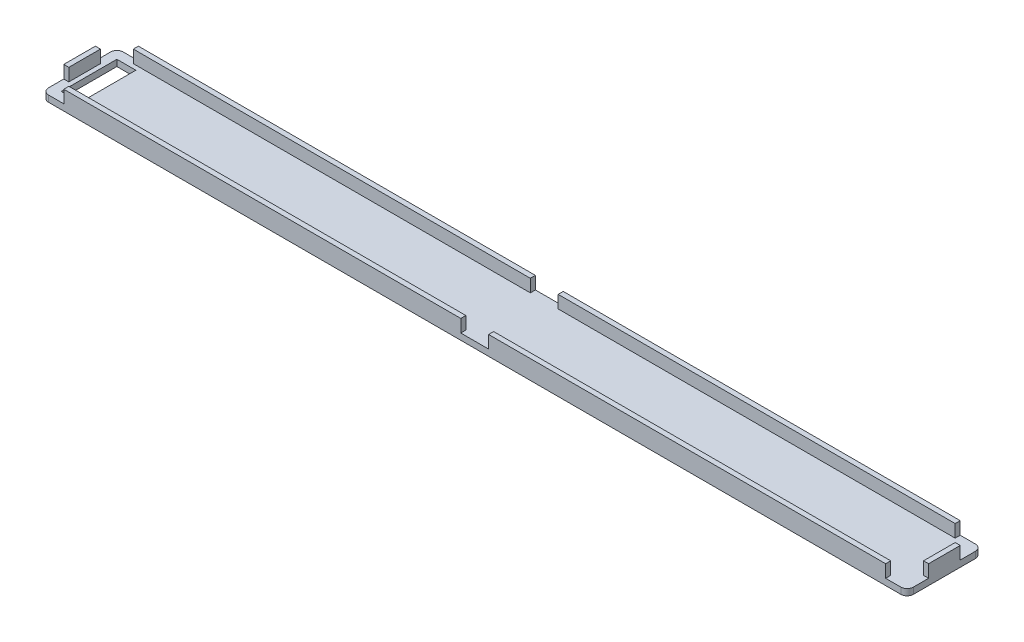
SolidWorks part; units mm, degrees
ref_plane "Plan de face" through (0, 0, 0) normal (0, 0, 1) x (1, 0, 0)
ref_plane "Plan de dessus" through (0, 0, 0) normal (0, 1, 0) x (1, 0, 0)
ref_plane "Plan de droite" through (0, 0, 0) normal (1, 0, 0) x (0, 0, -1)
sketch "Esquisse1" plane through (0, 0, 0) normal (0, 1, 0) x (1, 0, 0)
  line L1 (0, 0) -> (136.8, 0)
  line L2 (0, 0) -> (0, 11.8)
  line L3 (0, 11.8) -> (136.8, 11.8)
  line L4 (136.8, 0) -> (136.8, 11.8)
  dimension "D1" = 11.8
  dimension "D2" = 136.8
extrude "Boss.-Extru.1" add sketch "Esquisse1" along normal blind 1
sketch "Esquisse4" plane through (0, 1, 0) normal (0, 1, 0) x (1, 0, 0)
  line L0 (136, 11) -> (136, 0.8)
  line L1 (136.8, 11.8) -> (0, 11.8)
  line L2 (136.8, 11.8) -> (136.8, 0)
  line L3 (136.8, 0) -> (0, 0)
  line L4 (0, 11.8) -> (0, 0)
  line L5 (136, 0.8) -> (0.8, 0.8)
  line L6 (0.8, 11) -> (0.8, 0.8)
  line L7 (136, 11) -> (0.8, 11)
  dimension "D1" = 0.8
extrude "Boss.-Extru.3" add sketch "Esquisse4" along normal blind 2
sketch "Esquisse5" plane through (0, 3, 0) normal (0, 1, 0) x (1, 0, 0)
  line L0 (136.8, 11.8) -> (136.8, 8.4)
  line L1 (136.8, 0) -> (136.8, 11.8) construction
  line L2 (136.8, 8.4) -> (136, 8.4)
  line L3 (136, 0.8) -> (136, 11) construction
  line L4 (136, 8.4) -> (136, 11)
  line L5 (136, 11) -> (133.4, 11)
  line L6 (136, 11) -> (0.8, 11) construction
  line L7 (133.4, 11) -> (133.4, 11.8)
  line L8 (136.8, 11.8) -> (0, 11.8) construction
  line L9 (133.4, 11.8) -> (136.8, 11.8)
  line L10 (136.8, 5.9) -> (0, 5.9) construction
  line L11 (0, 11.8) -> (0, 0) construction
  line L12 (0, 0) -> (136.8, 0) construction
  line L13 (68.4, 11.8) -> (68.4, 0) construction
  line L14 (3.4, 11.8) -> (0, 11.8)
  line L15 (70.6, 11.8) -> (66.2, 11.8)
  line L16 (70.6, 11.8) -> (70.6, 11)
  line L17 (70.6, 11) -> (66.2, 11)
  line L18 (66.2, 11.8) -> (66.2, 11)
  line L19 (3.4, 11) -> (3.4, 11.8)
  line L20 (0.8, 11) -> (3.4, 11)
  line L21 (0.8, 8.4) -> (0.8, 11)
  line L22 (0, 8.4) -> (0.8, 8.4)
  line L23 (0, 11.8) -> (0, 8.4)
  line L24 (0, 0) -> (0, 3.4)
  line L25 (0, 3.4) -> (0.8, 3.4)
  line L26 (0.8, 3.4) -> (0.8, 0.8)
  line L27 (0.8, 0.8) -> (3.4, 0.8)
  line L28 (3.4, 0.8) -> (3.4, 0)
  line L29 (66.2, 0) -> (66.2, 0.8)
  line L30 (70.6, 0.8) -> (66.2, 0.8)
  line L31 (70.6, 0) -> (70.6, 0.8)
  line L32 (70.6, 0) -> (66.2, 0)
  line L33 (3.4, 0) -> (0, 0)
  line L34 (133.4, 0) -> (136.8, 0)
  line L35 (133.4, 0.8) -> (133.4, 0)
  line L36 (136, 0.8) -> (133.4, 0.8)
  line L37 (136, 3.4) -> (136, 0.8)
  line L38 (136.8, 3.4) -> (136, 3.4)
  line L39 (136.8, 0) -> (136.8, 3.4)
  dimension "D1" = 3.4
  dimension "D2" = 2.2
  dimension "D3" = 2.2
extrude "Enlèv. mat.-Extru.3" cut sketch "Esquisse5" against normal blind 2
sketch "Esquisse6" plane through (0, 0, 0) normal (0, -1, 0) x (1, 0, 0)
  line L0 (0, 0) -> (136.8, 0) construction
  line L1 (4.5, -1.5) -> (1.5, -1.5)
  line L2 (4.5, -1.5) -> (4.5, -10.3)
  line L3 (4.5, -10.3) -> (1.5, -10.3)
  line L4 (1.5, -1.5) -> (1.5, -10.3)
  line L5 (136.8, -11.8) -> (0, -11.8) construction
  line L6 (0, -11.8) -> (0, 0) construction
  dimension "D1" = 3
  dimension "D2" = 1.5
  dimension "D3" = 1.5
  dimension "D4" = 1.5
extrude "Enlèv. mat.-Extru.4" cut sketch "Esquisse6" against normal through all
fillet "Congé1" radius 1 4 edges at (136.8, 0.5, 0) (136.8, 0.5, -11.8) (0, 0.5, -11.8) (0, 0.5, 0)
